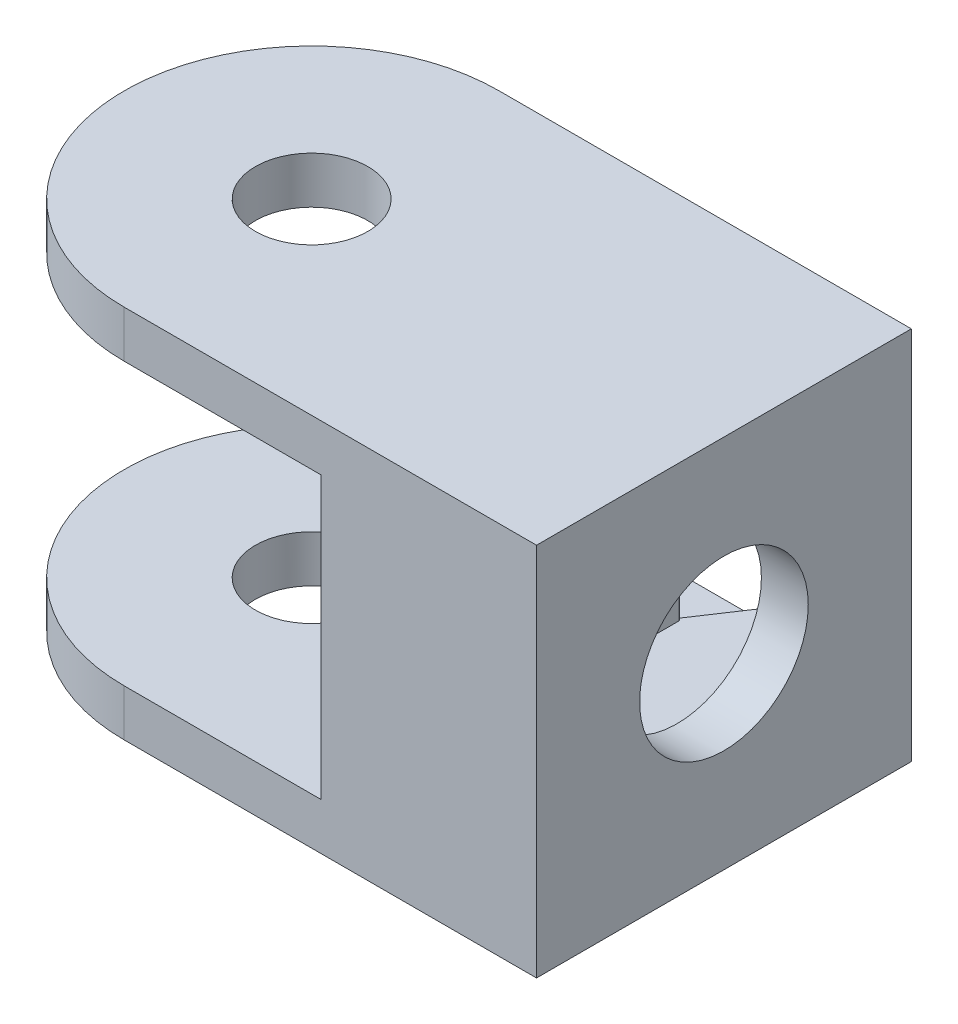
SolidWorks part; units mm, degrees
material "ABS"
ref_plane "Front Plane" through (0, 0, 0) normal (0, 0, 1) x (1, 0, 0)
ref_plane "Top Plane" through (0, 0, 0) normal (0, 1, 0) x (1, 0, 0)
ref_plane "Right Plane" through (0, 0, 0) normal (1, 0, 0) x (0, 0, -1)
sketch "Sketch1" plane through (0, 0, 0) normal (0, 1, 0) x (1, 0, 0)
  line L1 (-11, -10) -> (11, -10)
  line L3 (-11, 10) -> (11, 10)
  line L4 (11, -10) -> (11, 10)
  line L5 (-11, -10) -> (11, 10) construction
  line L6 (-11, 10) -> (11, -10) construction
  arc A0 (-11, 10) -> (-11, -10) centre (-11, 0) ccw
  circle A1 centre (-11, 0) radius 3
  point P0 (0, 0)
  dimension "D1" = 10
  dimension "D3" = 6
  dimension "D2" = 22
extrude "Boss-Extrude1" add sketch "Sketch1" along normal blind 20
sketch "Sketch4" plane through (0, 0, -10) normal (0, 0, -1) x (-1, 0, 0)
  line L0 (-11, 10) -> (-1.534, 10) construction
  line L1 (-8.5, 16.8) -> (-1.5, 16.8)
  line L2 (-8.5, 16.8) -> (-8.5, 3.2)
  line L3 (-8.5, 3.2) -> (-1.5, 3.2)
  line L4 (-1.5, 16.8) -> (-1.5, 3.2)
  line L5 (-11, 20) -> (-11, 0) construction
  dimension "D1" = 13.6
  dimension "D2" = 7
  dimension "D3" = 2.5
extrude "Cut-Extrude3" cut sketch "Sketch4" against normal blind 17
sketch "Sketch5" plane through (11, 0, 0) normal (1, 0, 0) x (0, 0, -1)
  line L0 (-10, 10) -> (10, 10) construction
  line L1 (-10, 20) -> (-10, 0) construction
  line L2 (10, 20) -> (10, 0) construction
  line L3 (0, 0) -> (0, 20) construction
  line L4 (-10, 0) -> (10, 0) construction
  line L5 (-10, 20) -> (10, 20) construction
  circle A0 centre (0, 10) radius 4.5
  dimension "D1" = 9
extrude "Cut-Extrude4" cut sketch "Sketch5" against normal up to next
ref_plane "Plane1" through (-11, 0, 0) normal (1, 0, 0) x (0, -1, 0)
sketch "Sketch7" plane through (-11, 0, 0) normal (1, 0, 0) x (0, -1, 0)
  line L0 (-20, 10) -> (0, 10) construction
  line L1 (-17.5, 10) -> (-2.5, 10)
  line L2 (-17.5, 10) -> (-17.5, -10)
  line L3 (-17.5, -10) -> (-2.5, -10)
  line L4 (-2.5, 10) -> (-2.5, -10)
  line L5 (-20, -10) -> (0, -10) construction
  line L6 (-10, 10) -> (-10, -10) construction
  dimension "D1" = 15
extrude "Cut-Extrude5" cut sketch "Sketch7" against normal mid plane 21
sketch "Sketch8" plane through (0, 0, 0) normal (0, -1, 0) x (1, 0, 0)
  line L0 (3.2151, -10) -> (-0.5, -4.4105)
  line L1 (11, -10) -> (-11, -10) construction
  line L2 (-0.5, -4.4105) -> (-0.5, -10)
  line L3 (-0.5, -10) -> (3.2151, -10)
  dimension "D1" = 56.39
  dimension "D2" = 5.5895
extrude "Cut-Extrude6" cut sketch "Sketch8" against normal blind 15 from offset 2.5 offset against normal yes
fillet "Fillet1" radius 0.1 1 edges at (1.5, 10, -7.4196)
